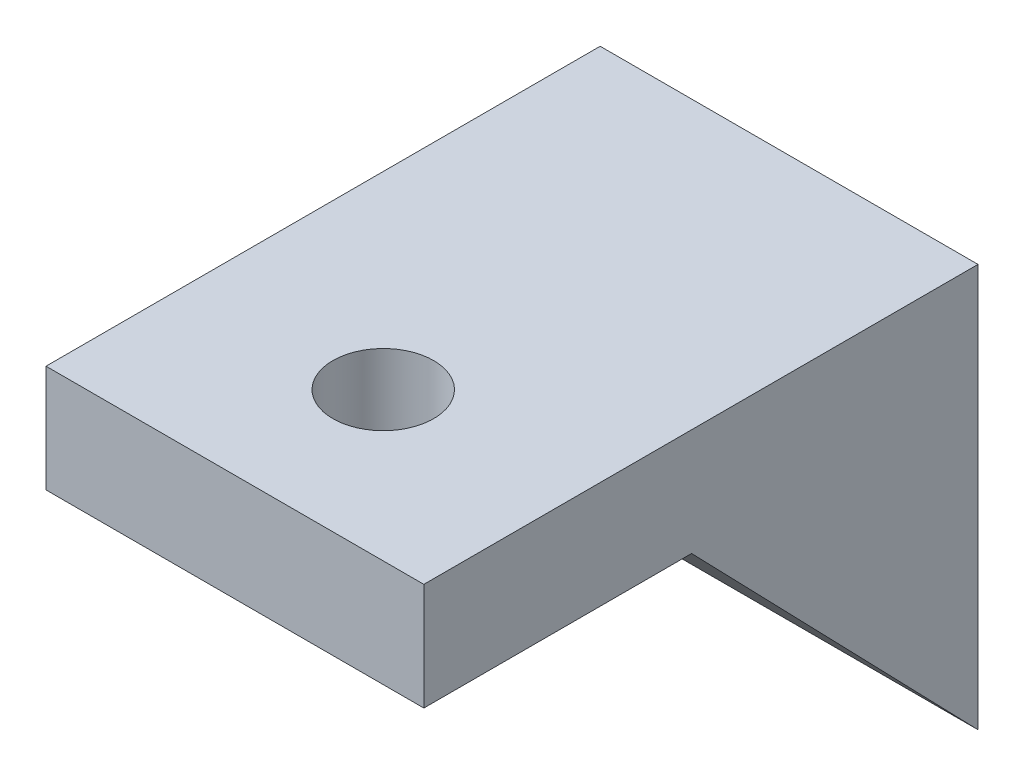
SolidWorks part; units mm, degrees
ref_plane "Front Plane" through (0, 0, 0) normal (0, 0, 1) x (1, 0, 0)
ref_plane "Top Plane" through (0, 0, 0) normal (0, 1, 0) x (1, 0, 0)
ref_plane "Right Plane" through (0, 0, 0) normal (1, 0, 0) x (0, 0, -1)
sketch "Sketch1" plane through (0, 0, 0) normal (0, 0, 1) x (1, 0, 0)
  line L1 (7.5, -8) -> (-7.5, -8)
  line L2 (7.5, -8) -> (7.5, 8)
  line L3 (7.5, 8) -> (-7.5, 8)
  line L4 (-7.5, -8) -> (-7.5, 8)
  line L5 (7.5, -8) -> (-7.5, 8) construction
  line L6 (7.5, 8) -> (-7.5, -8) construction
  point P0 (0, 0)
  dimension "D1" = 15
  dimension "D2" = 16
extrude "Boss-Extrude1" add sketch "Sketch1" along normal blind 22
sketch "Sketch4" plane through (0, 0, 0) normal (1, 0, 0) x (0, 0, -1)
  line L0 (-22, 3.7457) -> (-11.3699, 3.7457)
  line L1 (-22, -8) -> (-22, 8) construction
  line L2 (-11.3699, 3.7457) -> (0, -8)
  line L3 (0, -8) -> (-22, -8)
  line L4 (-22, -8) -> (-22, 3.7457)
extrude "Cut-Extrude1" cut sketch "Sketch4" against normal blind 22 and the other way blind 22
sketch "Sketch6" plane through (0, 8, 0) normal (0, 1, 0) x (1, 0, 0)
  line L0 (0, -8.8) -> (0, 8.8) construction
  circle A0 centre (0, -16.1107) radius 2
  dimension "D1" = 4
extrude "Cut-Extrude2" cut sketch "Sketch6" against normal blind 22
sketch "Sketch7" plane through (0, 0, 0) normal (0, 0, -1) x (-1, 0, 0)
  circle A0 centre (0, 0) radius 2
  dimension "D1" = 4
extrude "Cut-Extrude3" cut sketch "Sketch7" against normal blind 10
